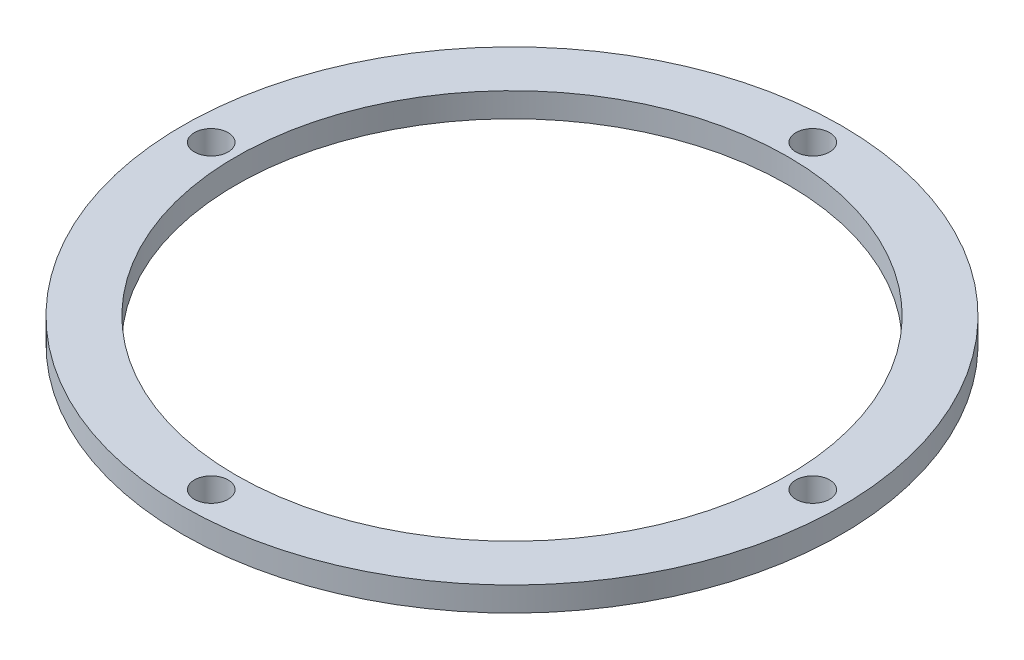
SolidWorks part; units mm, degrees
ref_plane "Front Plane" through (0, 0, 0) normal (0, 0, 1) x (1, 0, 0)
ref_plane "Top Plane" through (0, 0, 0) normal (0, 1, 0) x (1, 0, 0)
ref_plane "Right Plane" through (0, 0, 0) normal (1, 0, 0) x (0, 0, -1)
sketch "Sketch1" plane through (0, 0, 0) normal (0, 1, 0) x (1, 0, 0)
  circle A0 centre (0, 0) radius 86
  circle A1 centre (0, 0) radius 72
  circle A2 centre (0, 78.4889) radius 4.4
  circle A3 centre (78.4889, 0) radius 4.4
  circle A4 centre (0, -78.4889) radius 4.4
  circle A5 centre (-78.4889, 0) radius 4.4
  point P15 (0, 0)
  dimension "D1" = 172
  dimension "D2" = 144
  dimension "D3" = 8.8
  dimension "D4" = 78.4889
  dimension "D5" = 4
extrude "Boss-Extrude1" add sketch "Sketch1" along normal blind 6.35
